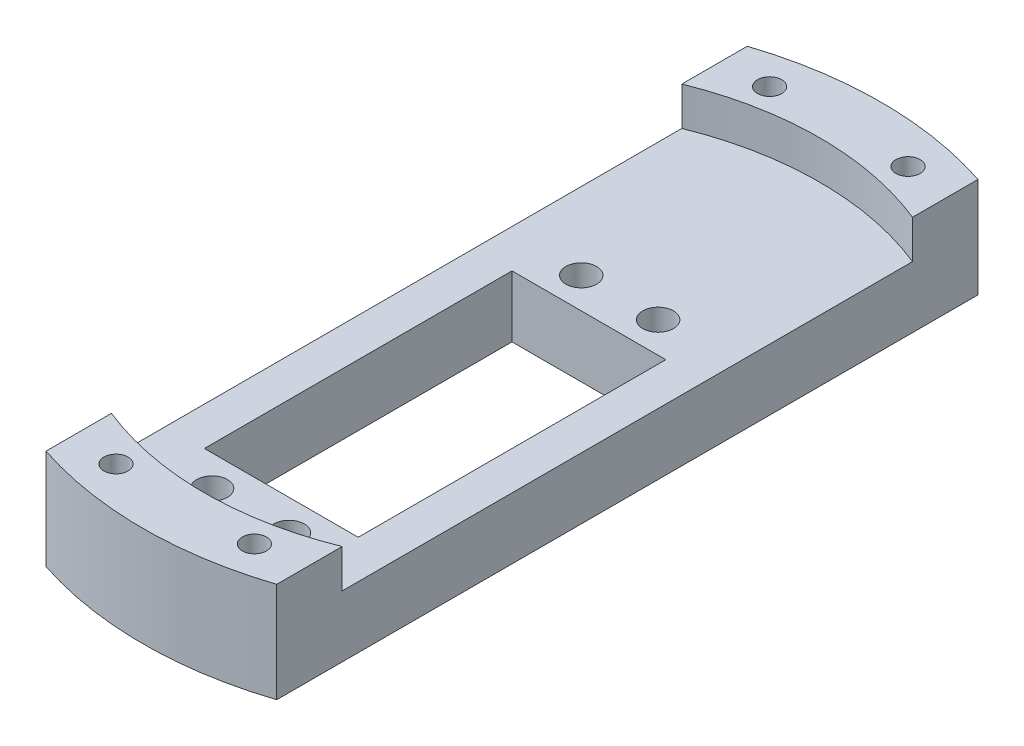
SolidWorks part; units mm, degrees
material "ABS"
ref_plane "Спереди" through (0, 0, 0) normal (0, 0, 1) x (1, 0, 0)
ref_plane "Сверху" through (0, 0, 0) normal (0, 1, 0) x (1, 0, 0)
ref_plane "Справа" through (0, 0, 0) normal (1, 0, 0) x (0, 0, -1)
sketch "Эскиз1" plane through (0, 0, 0) normal (0, 1, 0) x (1, 0, 0)
  line L0 (0, 0) -> (0, -69.818) construction
  line L1 (-1000, -10) -> (49000, -10) construction
  line L2 (-10, -30) -> (10, -30)
  line L3 (-10, -30) -> (-10, 10)
  line L4 (-10, 10) -> (10, 10)
  line L5 (10, -30) -> (10, 10)
  line L6 (-10, -30) -> (10, 10) construction
  line L7 (-10, 10) -> (10, -30) construction
  line L8 (-1000, 0) -> (49000, 0) construction
  line L9 (-15, -45.5961) -> (-15, 45.5961)
  line L10 (15, -45.5961) -> (15, 45.5961)
  arc A0 (-15, -45.5961) -> (15, -45.5961) centre (0, 0) ccw
  circle A1 centre (-5, -34) radius 2
  circle A2 centre (5, -34) radius 2
  circle A3 centre (5, 14) radius 2
  circle A4 centre (-5, 14) radius 2
  arc A5 (15, 45.5961) -> (-15, 45.5961) centre (0, 0) ccw
  point P3 (0, -10)
  dimension "D1" = 48
  dimension "D5" = 4
  dimension "D10" = 48
  dimension "D2" = 10
  dimension "D3" = 40
  dimension "D4" = 20
  dimension "D6" = 24
  dimension "D7" = 5
  dimension "D8" = 15
  dimension "D9" = 15
extrude "Бобышка-Вытянуть1" add sketch "Эскиз1" along normal blind 8
sketch "Эскиз2" plane through (0, 8, 0) normal (0, 1, 0) x (1, 0, 0)
  line L0 (-15, 37.081) -> (-15, 45.5961)
  line L1 (-15, 45.5961) -> (-15, -45.5961) construction
  line L2 (15, 45.5961) -> (15, 37.081)
  line L3 (15, -45.5961) -> (15, 45.5961) construction
  line L4 (-15, -37.081) -> (-15, -45.5961)
  line L5 (15, -37.081) -> (15, -45.5961)
  arc A0 (-15, -45.5961) -> (15, -45.5961) centre (0, 0) ccw
  arc A1 (-15, -37.081) -> (15, -37.081) centre (0, 0) ccw
  arc A2 (15, 37.081) -> (-15, 37.081) centre (0, 0) ccw
  arc A3 (15, 45.5961) -> (-15, 45.5961) centre (0, 0) ccw
  dimension "D1" = 30
  dimension "D2" = 80
  dimension "D3" = 48
extrude "Бобышка-Вытянуть2" add sketch "Эскиз2" along normal blind 5
hole_wizard "Сверло под метчик  спиральное M31" positions "Эскиз6" profile "Эскиз7" hole size "M3x0.5" standard "DIN" end condition through all
sketch "Эскиз6" plane through (0, 13, 0) normal (0, 1, 0) x (1, 0, 0)
  point P0 (-9, -42.5)
  dimension "D1" = 9
  dimension "D2" = 42.5
sketch "Эскиз7" plane through (-9, 13, 42.5) normal (1, 0, 0) x (0, 0, 1)
  line L0 (0, 0) -> (0, 13)
  line L1 (0, 13) -> (1.575, 13)
  line L2 (1.575, 13) -> (1.575, 0)
  line L5 (1.575, 0) -> (0, 0)
  line L11 (0, -6.35) -> (0, 107.95) construction
  dimension "Диаметр сквозного отверстия" = 3.15
  dimension "Глубина сквозного отверстия" = 13
sketch "Эскиз8" plane through (0, 0, 0) normal (0, 1, 0) x (1, 0, 0)
  line L0 (0, 0) -> (33.0205, 0) construction
  line L1 (0, 0) -> (0, -18.8534) construction
pattern_linear "Линейный массив1" count 2 spacing 18 along (1, 0, 0) count 2 spacing 85 along (0, 0, -1) of "Сверло под метчик  спиральное M31"
